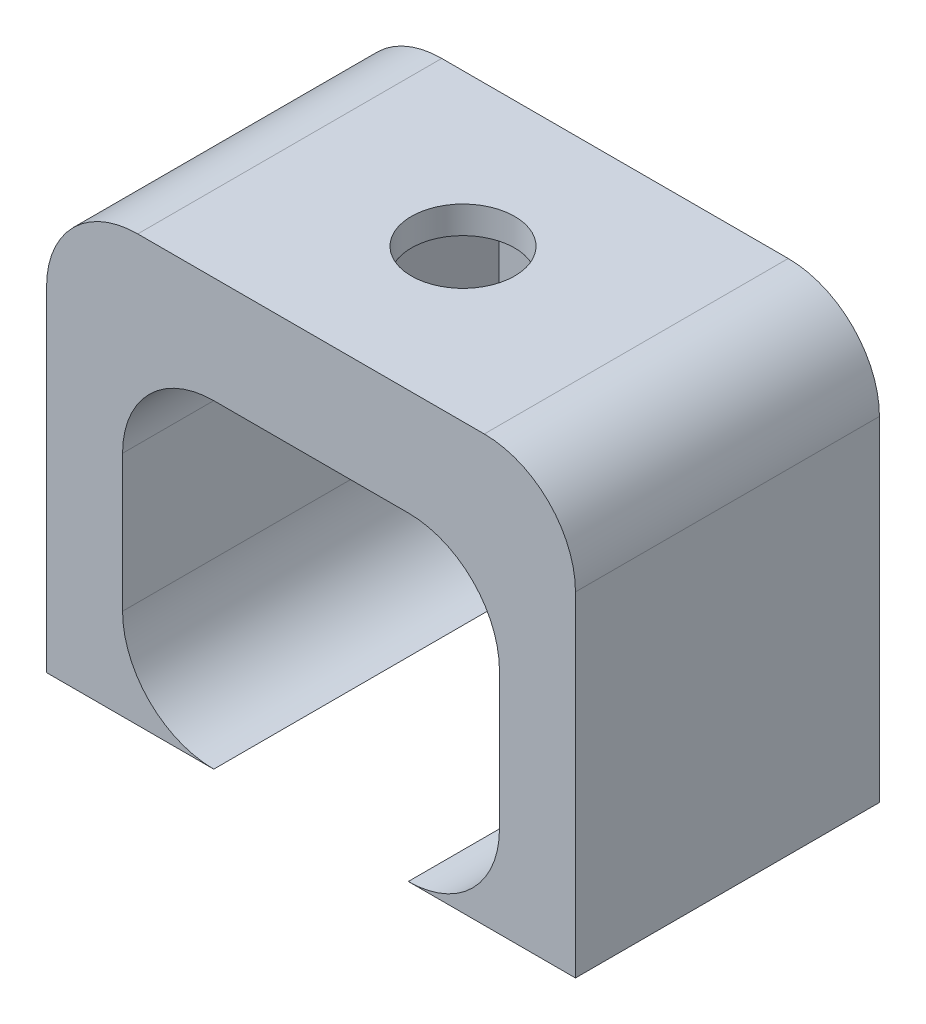
SolidWorks part; units mm, degrees
ref_plane "Plano frontal" through (0, 0, 0) normal (0, 0, 1) x (1, 0, 0)
ref_plane "Plano superior" through (0, 0, 0) normal (0, 1, 0) x (1, 0, 0)
ref_plane "Plano direito" through (0, 0, 0) normal (1, 0, 0) x (0, 0, -1)
sketch "Esboço1" plane through (0, 0, 0) normal (0, 0, 1) x (1, 0, 0)
  line L0 (3.2, -5.25) -> (8.7, -5.25)
  line L1 (-3.2, 5.25) -> (3.2, 5.25)
  line L2 (-6.2, 2.25) -> (-6.2, -2.25)
  line L4 (6.2, 2.25) -> (6.2, -2.25)
  line L5 (-6.2, 5.25) -> (6.2, -5.25) construction
  line L6 (-6.2, -5.25) -> (6.2, 5.25) construction
  line L7 (-8.7, 8.75) -> (8.7, 8.75)
  line L8 (-8.7, 8.75) -> (-8.7, -5.25)
  line L9 (-8.7, -5.25) -> (-3.2, -5.25)
  line L10 (8.7, 8.75) -> (8.7, -5.25)
  line L11 (-8.7, 8.75) -> (8.7, -5.25) construction
  line L12 (-8.7, -5.25) -> (8.7, 8.75) construction
  arc A0 (-6.2, -2.25) -> (-3.2, -5.25) centre (-3.2, -2.25) ccw
  arc A1 (3.2, -5.25) -> (6.2, -2.25) centre (3.2, -2.25) ccw
  arc A2 (3.2, 5.25) -> (6.2, 2.25) centre (3.2, 2.25) cw
  arc A3 (-3.2, 5.25) -> (-6.2, 2.25) centre (-3.2, 2.25) ccw
  point P0 (0, 0)
  point P6 (0, 0)
  point P19 (0, 1.75)
  point P24 (0, 0)
  point P25 (5.95, -5.25)
  point P26 (0, 0)
  point P27 (0, 0)
  point P28 (-4.2, -3.0148)
  point P29 (4.1974, -3.0092)
  point P30 (0, 0)
  point P31 (-1.3481, 3.1104)
  point P32 (0, 0)
  point P33 (0, 0)
  dimension "D3" = 3
  dimension "D1" = 12.4
  dimension "D2" = 10.5
  dimension "D4" = 3.5
  dimension "D5" = 2.5
extrude "Ressalto-extrusão1" add sketch "Esboço1" along normal blind 10
sketch "Esboço2" plane through (0, 5.25, 0) normal (0, -1, 0) x (1, 0, 0)
  line L0 (0, 0) -> (0, 10) construction
  line L1 (1.6166, 2.2) -> (3.2332, 5)
  line L2 (3.2332, 5) -> (1.6166, 7.8)
  line L3 (1.6166, 7.8) -> (-1.6166, 7.8)
  line L4 (-1.6166, 7.8) -> (-3.2332, 5)
  line L5 (-3.2332, 5) -> (-1.6166, 2.2)
  line L6 (-1.6166, 2.2) -> (1.6166, 2.2)
  line L7 (-3.2, 10) -> (3.2, 10) construction
  circle A0 centre (0, 5) radius 2.8 construction
  point P1 (0.0115, 3)
  point P14 (1.7561, 5.7221)
  dimension "D1" = 5.6
extrude "Corte-extrusão1" cut sketch "Esboço2" against normal blind 2.6 and the other way blind 2
sketch "Esboço3" plane through (0, 7.85, 0) normal (0, -1, 0) x (1, 0, 0)
  line L0 (1.6166, 7.8) -> (-1.6166, 7.8) construction
  circle A0 centre (0, 5) radius 1.7
  point P2 (0, 0)
  point P4 (0, 0)
  point P7 (0, 7.8)
  dimension "D1" = 3.4
extrude "Corte-extrusão2" cut sketch "Esboço3" against normal through all
sketch "Esboço4" plane through (0, -5.25, 0) normal (0, -1, 0) x (1, 0, 0)
  line L1 (-8.7, 10) -> (8.7, 10)
  line L2 (-8.7, 10) -> (-8.7, 0)
  line L3 (-8.7, 0) -> (8.7, 0)
  line L4 (8.7, 10) -> (8.7, 0)
extrude "Ressalto-extrusão2" [suppressed] add sketch "Esboço4" along normal blind 0.5
fillet "Filete2" radius 3 2 edges at (8.7, 8.75, 5) (-8.7, 8.75, 5)
